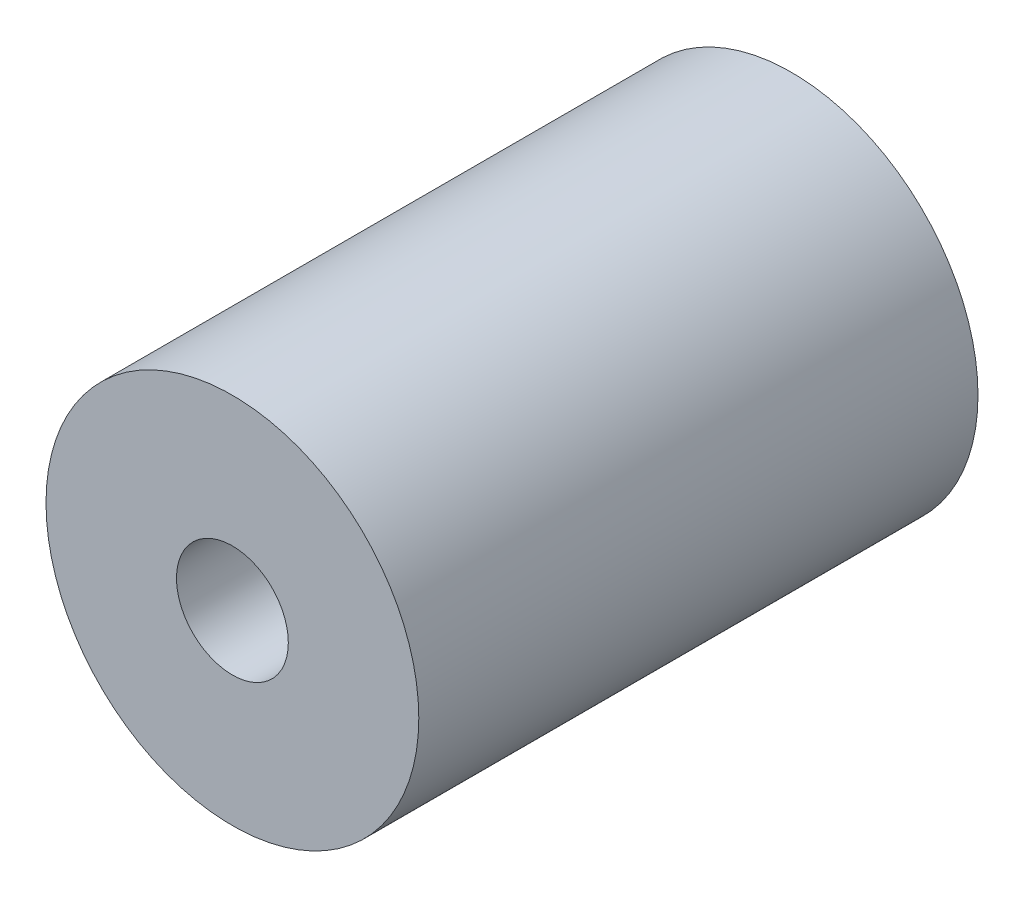
SolidWorks part; units mm, degrees
ref_plane "Front Plane" through (0, 0, 0) normal (0, 0, 1) x (1, 0, 0)
ref_plane "Top Plane" through (0, 0, 0) normal (0, 1, 0) x (1, 0, 0)
ref_plane "Right Plane" through (0, 0, 0) normal (1, 0, 0) x (0, 0, -1)
sketch "Sketch1" plane through (0, 0, 0) normal (0, 0, 1) x (1, 0, 0)
  circle A0 centre (0, 0) radius 5
  dimension "D1" = 10
extrude "Boss-Extrude1" add sketch "Sketch1" along normal blind 15
sketch "Sketch2" plane through (0, 0, 15) normal (0, 0, 1) x (1, 0, 0)
  circle A0 centre (0, 0) radius 1.5
  dimension "D1" = 3
extrude "Cut-Extrude1" cut sketch "Sketch2" against normal blind 20
